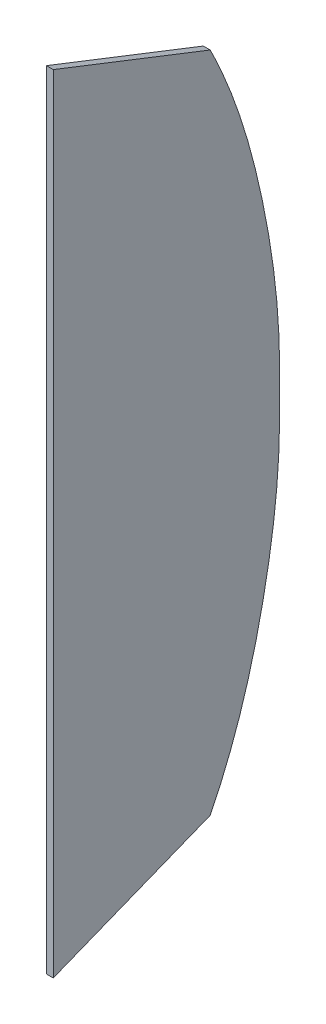
SolidWorks part; units mm, degrees
ref_plane "Спереди" through (0, 0, 0) normal (0, 0, 1) x (1, 0, 0)
ref_plane "Сверху" through (0, 0, 0) normal (0, 1, 0) x (1, 0, 0)
ref_plane "Справа" through (0, 0, 0) normal (1, 0, 0) x (0, 0, -1)
sketch "Эскиз1" plane through (0, 0, 0) normal (1, 0, 0) x (0, 0, -1)
  line L0 (-455, -523) -> (-455, 523) construction
  line L1 (-243, -438.6617) -> (-243, 440) construction
  line L2 (-455, -516.5426) -> (-455, 516.5565)
  line L3 (-455, 516.5565) -> (-249, 435.9056)
  line L4 (-455, -516.5426) -> (-249, -434.5913)
  line L5 (-449, 514.2075) -> (-249, 435.9056) construction
  line L6 (-449, -514.1557) -> (-449, 514.2075) construction
  line L7 (-449, -514.1557) -> (-249, -434.5913) construction
  line L8 (-455, -523) -> (-243, -438.6617) construction
  line L9 (-249, -434.5913) -> (-249, 435.9056) construction
  line L10 (-455, 523) -> (-243, 440) construction
  spline S2 degree 3 poles (-249, 435.9056) (-244.8122, 427.5807) (-236.8014, 410.7383) (-222.2124, 376.4639) (-206.4721, 332.5736) (-191.0652, 278.6225) (-178.6184, 223.742) (-168.6012, 168.3762) (-162.6642, 121.9958) (-159.5885, 84.7804) (-158.191, 56.8473) (-157.6991, 28.8204) (-157.6682, 0.6571) (-157.6991, -27.5061) (-158.191, -55.533) (-159.5885, -83.4661) (-162.6642, -120.6815) (-168.6012, -167.0619) (-178.6184, -222.4277) (-191.0652, -277.3082) (-206.4721, -331.2593) (-222.2124, -375.1496) (-236.8014, -409.424) (-244.8122, -426.2664) (-249, -434.5913) knots 0.002534 0.002534 0.002534 0.002534 0.033626 0.064718 0.126901 0.189084 0.251267 0.31345 0.375634 0.406725 0.437817 0.468908 0.5 0.531092 0.562183 0.593275 0.624366 0.68655 0.748733 0.810916 0.873099 0.935282 0.966374 0.997466 0.997466 0.997466 0.997466
  dimension "D1" = 6
extrude "Бобышка-Вытянуть2" add sketch "Эскиз1" along normal blind 9
